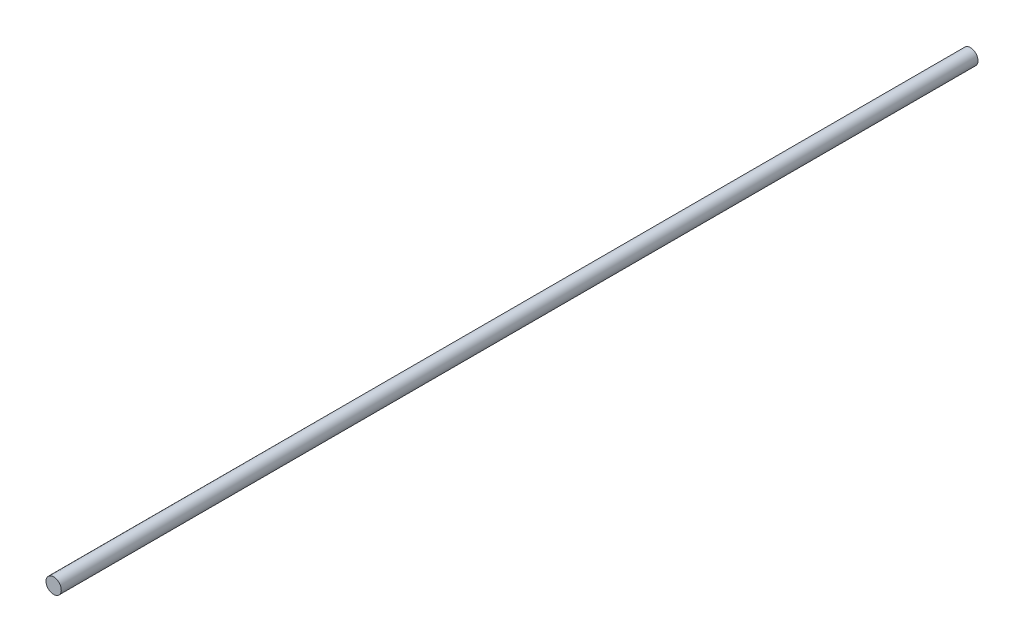
SolidWorks part; units mm, degrees
material "AISI 1010 Steel, hot rolled bar"
ref_plane "Front Plane" through (0, 0, 0) normal (0, 0, 1) x (1, 0, 0)
ref_plane "Top Plane" through (0, 0, 0) normal (0, 1, 0) x (1, 0, 0)
ref_plane "Right Plane" through (0, 0, 0) normal (1, 0, 0) x (0, 0, -1)
sketch "Sketch1" plane through (0, 0, 0) normal (0, 0, 1) x (1, 0, 0)
  circle A0 centre (0, 0) radius 5
  dimension "D1" = 10
extrude "Boss-Extrude1" add sketch "Sketch1" along normal mid plane 600
